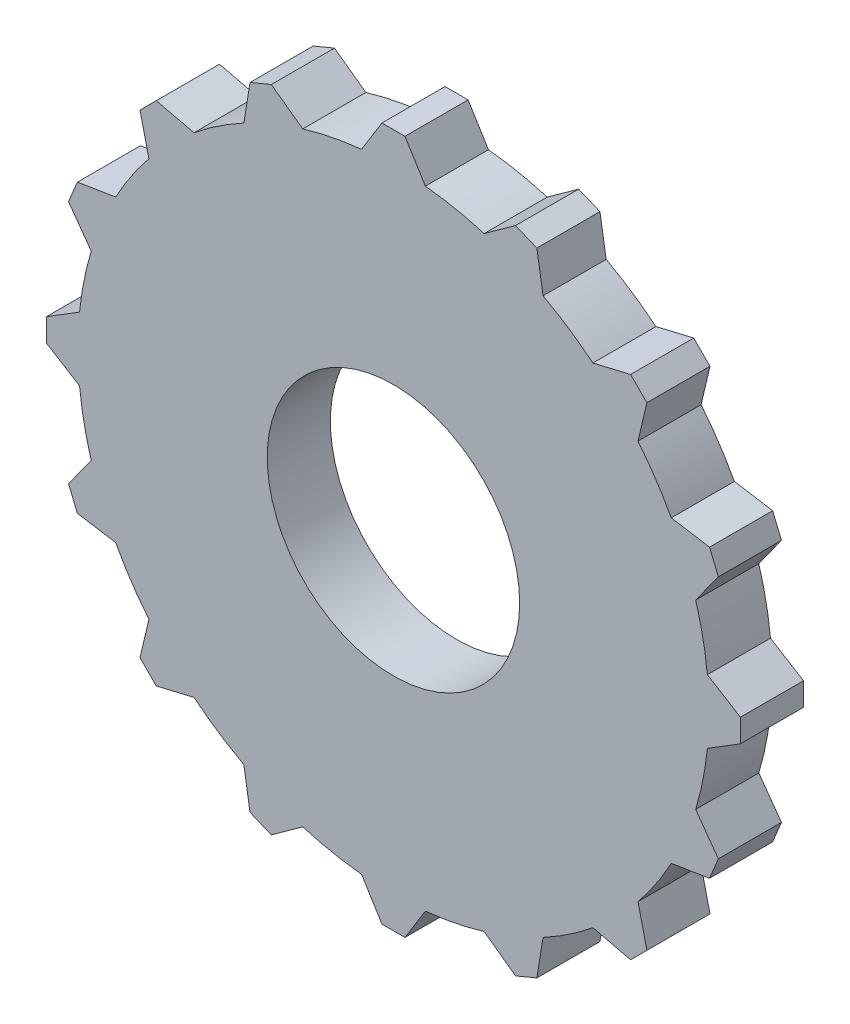
SolidWorks part; units mm, degrees
ref_plane "Front Plane" through (0, 0, 0) normal (0, 0, 1) x (1, 0, 0)
ref_plane "Top Plane" through (0, 0, 0) normal (0, 1, 0) x (1, 0, 0)
ref_plane "Right Plane" through (0, 0, 0) normal (1, 0, 0) x (0, 0, -1)
sketch "Sketch1" plane through (0, 0, 0) normal (0, 0, 1) x (1, 0, 0)
  line L0 (1.8263, 54.9697) -> (-1.8263, 54.9697)
  line L3 (5.0555, 49.7438) -> (1.8263, 54.9697)
  line L6 (0, -60.5611) -> (0, 60.5611) construction
  line L9 (-5.0555, 49.7438) -> (-1.8263, 54.9697)
  line L10 (14.3654, 47.8919) -> (19.3487, 51.4843)
  line L11 (22.7233, 50.0865) -> (19.3487, 51.4843)
  line L12 (23.7068, 44.0226) -> (22.7233, 50.0865)
  line L13 (31.5993, 38.749) -> (37.578, 40.1608)
  line L14 (40.1608, 37.578) -> (37.578, 40.1608)
  line L15 (38.749, 31.5993) -> (40.1608, 37.578)
  line L16 (44.0226, 23.7068) -> (50.0865, 22.7233)
  line L17 (51.4843, 19.3487) -> (50.0865, 22.7233)
  line L18 (47.8919, 14.3654) -> (51.4843, 19.3487)
  line L19 (49.7438, 5.0555) -> (54.9697, 1.8263)
  line L20 (54.9697, -1.8263) -> (54.9697, 1.8263)
  line L21 (49.7438, -5.0555) -> (54.9697, -1.8263)
  line L22 (47.8919, -14.3654) -> (51.4843, -19.3487)
  line L23 (50.0865, -22.7233) -> (51.4843, -19.3487)
  line L24 (44.0226, -23.7068) -> (50.0865, -22.7233)
  line L25 (38.749, -31.5993) -> (40.1608, -37.578)
  line L26 (37.578, -40.1608) -> (40.1608, -37.578)
  line L27 (31.5993, -38.749) -> (37.578, -40.1608)
  line L28 (23.7068, -44.0226) -> (22.7233, -50.0865)
  line L29 (19.3487, -51.4843) -> (22.7233, -50.0865)
  line L30 (14.3654, -47.8919) -> (19.3487, -51.4843)
  line L31 (5.0555, -49.7438) -> (1.8263, -54.9697)
  line L32 (-1.8263, -54.9697) -> (1.8263, -54.9697)
  line L33 (-5.0555, -49.7438) -> (-1.8263, -54.9697)
  line L34 (-14.3654, -47.8919) -> (-19.3487, -51.4843)
  line L35 (-22.7233, -50.0865) -> (-19.3487, -51.4843)
  line L36 (-23.7068, -44.0226) -> (-22.7233, -50.0865)
  line L37 (-31.5993, -38.749) -> (-37.578, -40.1608)
  line L38 (-40.1608, -37.578) -> (-37.578, -40.1608)
  line L39 (-38.749, -31.5993) -> (-40.1608, -37.578)
  line L40 (-44.0226, -23.7068) -> (-50.0865, -22.7233)
  line L41 (-51.4843, -19.3487) -> (-50.0865, -22.7233)
  line L42 (-47.8919, -14.3654) -> (-51.4843, -19.3487)
  line L43 (-49.7438, -5.0555) -> (-54.9697, -1.8263)
  line L44 (-54.9697, 1.8263) -> (-54.9697, -1.8263)
  line L45 (-49.7438, 5.0555) -> (-54.9697, 1.8263)
  line L46 (-47.8919, 14.3654) -> (-51.4843, 19.3487)
  line L47 (-50.0865, 22.7233) -> (-51.4843, 19.3487)
  line L48 (-44.0226, 23.7068) -> (-50.0865, 22.7233)
  line L49 (-38.749, 31.5993) -> (-40.1608, 37.578)
  line L50 (-37.578, 40.1608) -> (-40.1608, 37.578)
  line L51 (-31.5993, 38.749) -> (-37.578, 40.1608)
  line L52 (-23.7068, 44.0226) -> (-22.7233, 50.0865)
  line L53 (-19.3487, 51.4843) -> (-22.7233, 50.0865)
  line L54 (-14.3654, 47.8919) -> (-19.3487, 51.4843)
  circle A0 centre (0, 0) radius 20
  circle A1 centre (0, 0) radius 40
  arc A2 (-23.7068, 44.0226) -> (-31.5993, 38.749) centre (0, 0) ccw
  arc A4 (-38.749, 31.5993) -> (-44.0226, 23.7068) centre (0, 0) ccw
  arc A5 (-47.8919, 14.3654) -> (-49.7438, 5.0555) centre (0, 0) ccw
  arc A6 (-49.7438, -5.0555) -> (-47.8919, -14.3654) centre (0, 0) ccw
  arc A7 (-44.0226, -23.7068) -> (-38.749, -31.5993) centre (0, 0) ccw
  arc A8 (-31.5993, -38.749) -> (-23.7068, -44.0226) centre (0, 0) ccw
  arc A9 (-14.3654, -47.8919) -> (-5.0555, -49.7438) centre (0, 0) ccw
  arc A10 (5.0555, -49.7438) -> (14.3654, -47.8919) centre (0, 0) ccw
  arc A11 (23.7068, -44.0226) -> (31.5993, -38.749) centre (0, 0) ccw
  arc A12 (38.749, -31.5993) -> (44.0226, -23.7068) centre (0, 0) ccw
  arc A13 (47.8919, -14.3654) -> (49.7438, -5.0555) centre (0, 0) ccw
  arc A14 (49.7438, 5.0555) -> (47.8919, 14.3654) centre (0, 0) ccw
  arc A15 (44.0226, 23.7068) -> (38.749, 31.5993) centre (0, 0) ccw
  arc A16 (31.5993, 38.749) -> (23.7068, 44.0226) centre (0, 0) ccw
  arc A17 (14.3654, 47.8919) -> (5.0555, 49.7438) centre (0, 0) ccw
  arc A18 (-5.0555, 49.7438) -> (-14.3654, 47.8919) centre (0, 0) ccw
  point P9 (0, 54.9697)
  point P74 (0, 0)
  point P92 (0, 0)
  dimension "D1" = 16
extrude "Boss-Extrude1" add sketch "Sketch1" along normal blind 10 contours L9 A18 L54 L53 L52 A2 L51 L50 L49 A4 L48 L47 L46 A5 L45 L44 L43 A6 L42 L41 L40 A7 L39 L38 L37 A8 L36 L35 L34 A9 L33 L32 L31 A10 L30 L29 L28 A11 L27 L26 L25 A12 L24 L23 L22 A13 L21 L20 L19 A14 L18 | A1 A0
